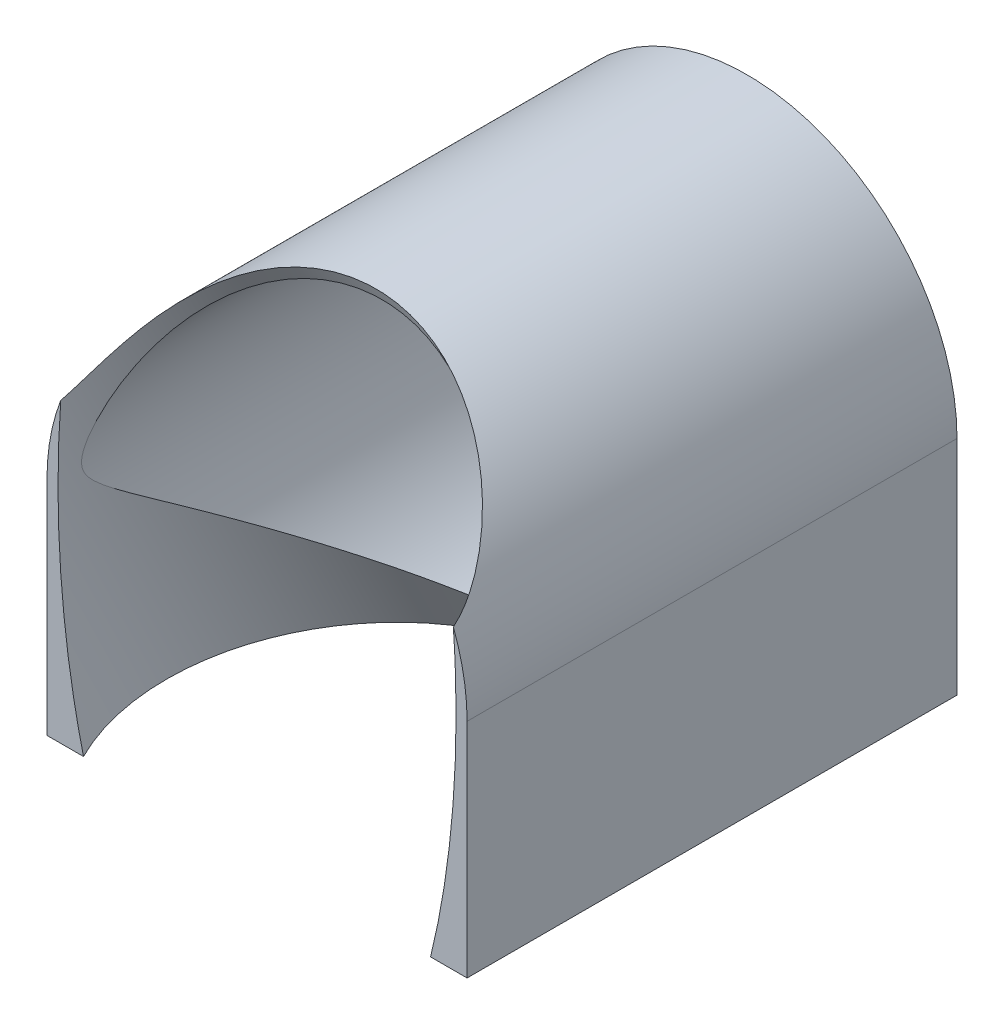
SolidWorks part; units mm, degrees
ref_plane "Front Plane" through (0, 0, 0) normal (0, 0, 1) x (1, 0, 0)
ref_plane "Top Plane" through (0, 0, 0) normal (0, 1, 0) x (1, 0, 0)
ref_plane "Right Plane" through (0, 0, 0) normal (1, 0, 0) x (0, 0, -1)
sketch "Sketch1" plane through (0, 0, 0) normal (0, 0, 1) x (1, 0, 0)
  circle A0 centre (0, 200) radius 15.85 construction
  circle A1 centre (0, 200) radius 15.85 construction
  circle A2 centre (0, 200) radius 16.15
  circle A3 centre (0, 200) radius 17.15
  dimension "D1" = 0.3
  dimension "D2" = 1.3
extrude "Boss-Extrude1" add sketch "Sketch1" against normal blind 40
sketch "Sketch4" plane through (0, 0, -40) normal (0, 0, -1) x (-1, 0, 0)
  line L0 (-17.15, 200) -> (-17.15, 182.85)
  line L1 (-17.15, 182.85) -> (0, 182.85)
  line L2 (0, 182.85) -> (17.15, 182.85)
  line L3 (17.15, 182.85) -> (17.15, 200)
  line L5 (-17.15, 182.85) -> (17.15, 182.85)
  line L6 (-17.15, 182.85) -> (-17.15, 181.85)
  line L7 (-17.15, 181.85) -> (17.15, 181.85)
  line L8 (17.15, 182.85) -> (17.15, 181.85)
  circle A0 centre (0, 200) radius 17.15 construction
  circle A1 centre (0, 200) radius 17.15
  point P10 (17.15, 182.85)
  circle M2 centre (0, 200) radius 17.15
  dimension "D1" = 1
extrude "Boss-Extrude3" add sketch "Sketch4" against normal blind 40 contours L8 L2 L1 L6 L7 | L2 L3 M2 | L0 L1 M2
sketch "Sketch2" plane through (0, 401.9752, 196.0564) normal (0, 0.8988, 0.4384) x (1, 0, 0)
  circle A0 centre (0, 87.6742) radius 16.25 construction
  circle A1 centre (0, 87.6742) radius 16.25
extrude "Cut-Extrude1" cut sketch "Sketch2" against normal through all
